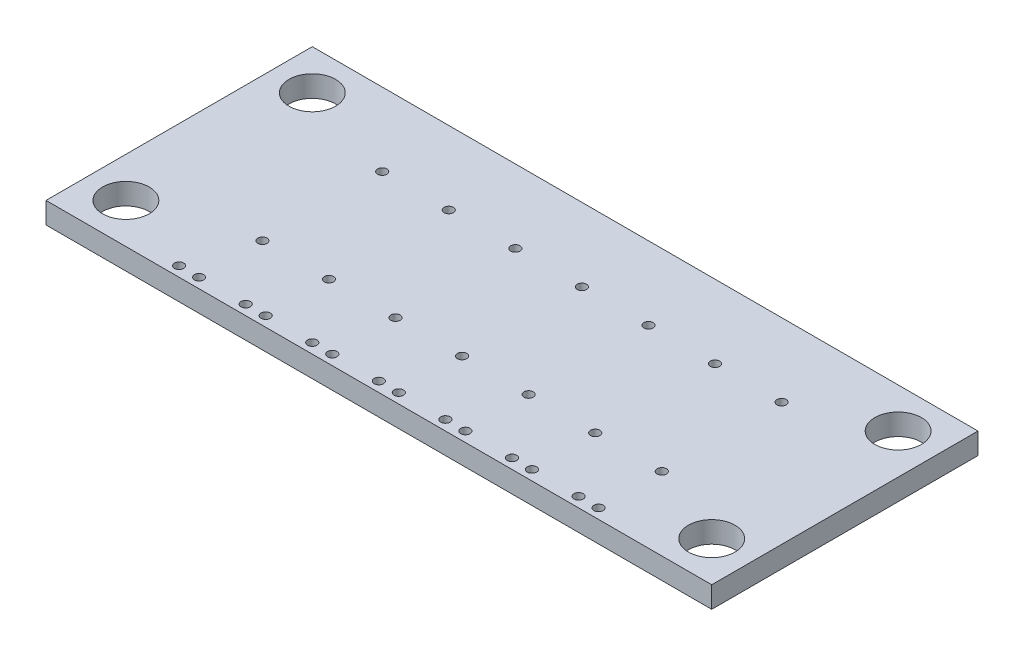
SolidWorks part; units mm, degrees
ref_plane "Front Plane" through (0, 0, 0) normal (0, 0, 1) x (1, 0, 0)
ref_plane "Top Plane" through (0, 0, 0) normal (0, 1, 0) x (1, 0, 0)
ref_plane "Right Plane" through (0, 0, 0) normal (1, 0, 0) x (0, 0, -1)
sketch "Sketch1" plane through (0, 0, 0) normal (0, 1, 0) x (1, 0, 0)
  line L1 (0, 0) -> (50, 0)
  line L2 (0, 0) -> (0, 20)
  line L3 (0, 20) -> (50, 20)
  line L4 (50, 0) -> (50, 20)
  circle A0 centre (3, 17) radius 1.75
  circle A1 centre (47, 3) radius 1.75
  circle A2 centre (3, 3) radius 1.75
  circle A3 centre (47, 17) radius 1.75
  dimension "D3" = 3.5
  dimension "D1" = 20
  dimension "D2" = 50
  dimension "D4" = 3
  dimension "D5" = 3
  dimension "D7" = 3
  dimension "D8" = 3
extrude "Boss-Extrude1" add sketch "Sketch1" along normal blind 1.6
sketch "Sketch2" plane through (0, 1.6, 0) normal (0, 1, 0) x (1, 0, 0)
  line L0 (50, 20) -> (0, 20) construction
  line L2 (8.5, 20) -> (8.5, 0)
  line L4 (11.5, 20) -> (11.5, 0)
  line L5 (0, 0) -> (50, 0) construction
  line L6 (0, 20) -> (0, 0) construction
  line L7 (10, 0) -> (10, 19.5)
  line L8 (10, 19.5) -> (8.5, 19.5)
  line L9 (11.5, 10) -> (10, 10)
  line L10 (16.5, 20) -> (16.5, 0)
  line L11 (15, 0) -> (15, 19.5)
  line L12 (13.5, 20) -> (13.5, 0)
  line L13 (16.5, 10) -> (15, 10)
  line L16 (15, 19.5) -> (13.5, 19.5)
  line L17 (21.5, 20) -> (21.5, 0)
  line L18 (20, 0) -> (20, 19.5)
  line L19 (18.5, 20) -> (18.5, 0)
  line L20 (21.5, 10) -> (20, 10)
  line L23 (20, 19.5) -> (18.5, 19.5)
  line L24 (26.5, 20) -> (26.5, 0)
  line L25 (25, 0) -> (25, 19.5)
  line L26 (23.5, 20) -> (23.5, 0)
  line L27 (26.5, 10) -> (25, 10)
  line L30 (25, 19.5) -> (23.5, 19.5)
  line L31 (31.5, 20) -> (31.5, 0)
  line L32 (30, 0) -> (30, 19.5)
  line L33 (28.5, 20) -> (28.5, 0)
  line L34 (31.5, 10) -> (30, 10)
  line L37 (30, 19.5) -> (28.5, 19.5)
  line L38 (36.5, 20) -> (36.5, 0)
  line L39 (35, 0) -> (35, 19.5)
  line L40 (33.5, 20) -> (33.5, 0)
  line L41 (36.5, 10) -> (35, 10)
  line L44 (35, 19.5) -> (33.5, 19.5)
  line L45 (41.5, 20) -> (41.5, 0)
  line L46 (40, 0) -> (40, 19.5)
  line L47 (38.5, 20) -> (38.5, 0)
  line L48 (41.5, 10) -> (40, 10)
  line L51 (40, 19.5) -> (38.5, 19.5)
  line L52 (8.5, 20.25) -> (11.5, 20.25)
  line L53 (8.5, 0) -> (11.5, 0)
  line L54 (8.5, 20) -> (8.5, 20.25)
  line L55 (11.5, 20) -> (11.5, 20.25)
  line L56 (13.5, 0) -> (16.5, 0)
  line L57 (13.5, 20.25) -> (16.5, 20.25)
  line L58 (16.5, 20) -> (16.5, 20.25)
  line L59 (13.5, 20) -> (13.5, 20.25)
  line L60 (18.5, 0) -> (21.5, 0)
  line L61 (18.5, 20.25) -> (21.5, 20.25)
  line L62 (21.5, 20) -> (21.5, 20.25)
  line L63 (18.5, 20) -> (18.5, 20.25)
  line L64 (23.5, 0) -> (26.5, 0)
  line L65 (23.5, 20.25) -> (26.5, 20.25)
  line L66 (26.5, 20) -> (26.5, 20.25)
  line L67 (23.5, 20) -> (23.5, 20.25)
  line L68 (28.5, 0) -> (31.5, 0)
  line L69 (28.5, 20.25) -> (31.5, 20.25)
  line L70 (31.5, 20) -> (31.5, 20.25)
  line L71 (28.5, 20) -> (28.5, 20.25)
  line L72 (33.5, 0) -> (36.5, 0)
  line L73 (33.5, 20.25) -> (36.5, 20.25)
  line L74 (36.5, 20) -> (36.5, 20.25)
  line L75 (33.5, 20) -> (33.5, 20.25)
  line L76 (38.5, 0) -> (41.5, 0)
  line L77 (38.5, 20.25) -> (41.5, 20.25)
  line L78 (41.5, 20) -> (41.5, 20.25)
  line L79 (38.5, 20) -> (38.5, 20.25)
  dimension "D1" = 8.5
  dimension "D2" = 3
  dimension "D3" = 0.25
  dimension "D4" = 7
  dimension "D5" = 7
sketch "Sketch3" plane through (0, 1.6, 0) normal (0, 1, 0) x (1, 0, 0)
  line L1 (11.5, 10) -> (10, 10) construction
  line L2 (10, 19.5) -> (8.5, 19.5) construction
  line L3 (10.75, 5.5) -> (10.75, 14.5) construction
  line L4 (9.25, 19.5) -> (9.25, 0.75) construction
  line L5 (0, 0) -> (50, 0) construction
  circle A0 centre (9.25, 0.75) radius 0.35
  circle A1 centre (10.75, 0.75) radius 0.35
  circle A2 centre (10.75, 5.5) radius 0.35
  circle A3 centre (10.75, 14.5) radius 0.35
  circle A4 centre (15.75, 5.5) radius 0.35
  circle A5 centre (15.75, 14.5) radius 0.35
  circle A6 centre (15.75, 0.75) radius 0.35
  circle A7 centre (14.25, 0.75) radius 0.35
  circle A8 centre (20.75, 5.5) radius 0.35
  circle A9 centre (20.75, 14.5) radius 0.35
  circle A10 centre (20.75, 0.75) radius 0.35
  circle A11 centre (19.25, 0.75) radius 0.35
  circle A12 centre (25.75, 5.5) radius 0.35
  circle A13 centre (25.75, 14.5) radius 0.35
  circle A14 centre (25.75, 0.75) radius 0.35
  circle A15 centre (24.25, 0.75) radius 0.35
  circle A16 centre (30.75, 5.5) radius 0.35
  circle A17 centre (30.75, 14.5) radius 0.35
  circle A18 centre (30.75, 0.75) radius 0.35
  circle A19 centre (29.25, 0.75) radius 0.35
  circle A20 centre (35.75, 5.5) radius 0.35
  circle A21 centre (35.75, 14.5) radius 0.35
  circle A22 centre (35.75, 0.75) radius 0.35
  circle A23 centre (34.25, 0.75) radius 0.35
  circle A24 centre (40.75, 5.5) radius 0.35
  circle A25 centre (40.75, 14.5) radius 0.35
  circle A26 centre (40.75, 0.75) radius 0.35
  circle A27 centre (39.25, 0.75) radius 0.35
  point P8 (9.25, 19.5)
  point P12 (10.75, 10)
  point P16 (10.75, 10)
  dimension "D1" = 0.7
  dimension "D3" = 9
  dimension "D2" = 0.75
  dimension "D4" = 7
extrude "Cut-Extrude1" cut sketch "Sketch3" against normal through all
